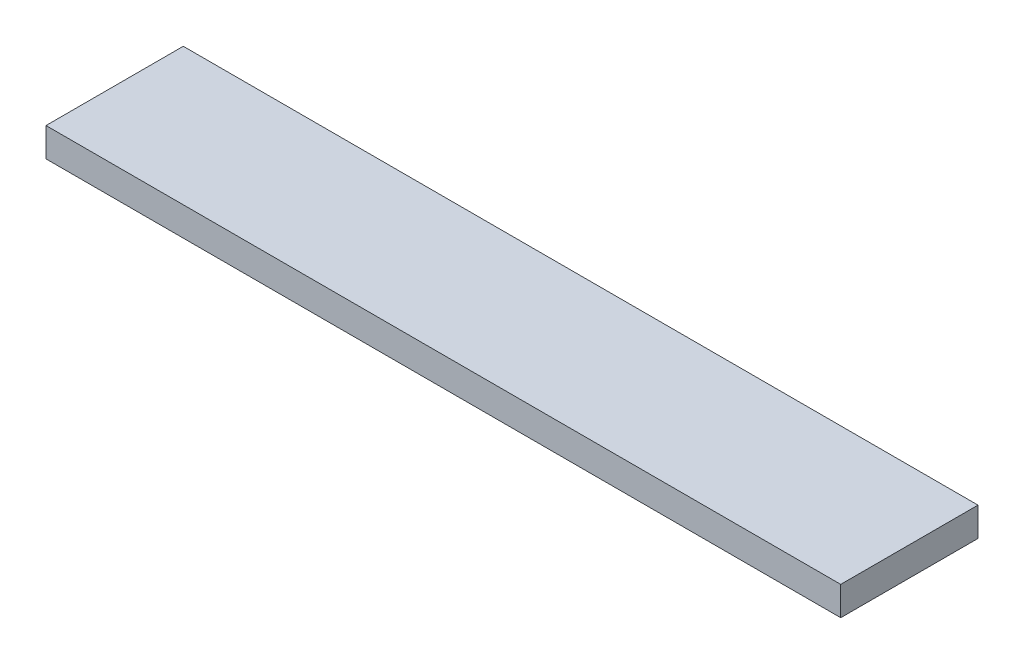
SolidWorks part; units mm, degrees
ref_plane "Front Plane" through (0, 0, 0) normal (0, 0, 1) x (1, 0, 0)
ref_plane "Top Plane" through (0, 0, 0) normal (0, 1, 0) x (1, 0, 0)
ref_plane "Right Plane" through (0, 0, 0) normal (1, 0, 0) x (0, 0, -1)
sketch "Sketch1" plane through (0, 0, 0) normal (0, 1, 0) x (1, 0, 0)
  line L1 (0, 0) -> (69.85, 0)
  line L2 (0, 0) -> (0, 12.065)
  line L3 (0, 12.065) -> (69.85, 12.065)
  line L4 (69.85, 0) -> (69.85, 12.065)
  dimension "D1" = 12.065
  dimension "D2" = 69.85
extrude "Boss-Extrude1" add sketch "Sketch1" along normal blind 2.54
